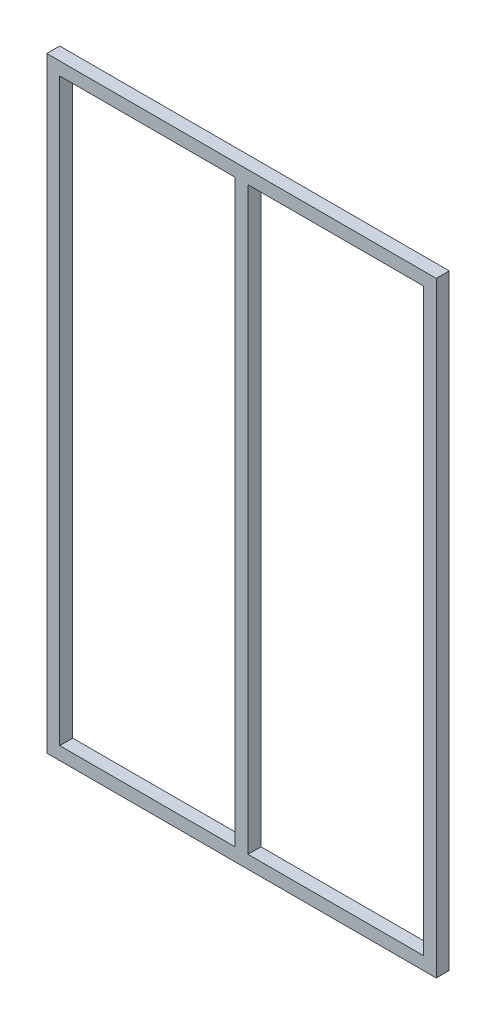
SolidWorks part; units mm, degrees
material "Cedar"
ref_plane "Front Plane" through (0, 0, 0) normal (0, 0, 1) x (1, 0, 0)
ref_plane "Top Plane" through (0, 0, 0) normal (0, 1, 0) x (1, 0, 0)
ref_plane "Right Plane" through (0, 0, 0) normal (1, 0, 0) x (0, 0, -1)
sketch "Sketch1" plane through (0, 0, 0) normal (0, 0, 1) x (1, 0, 0)
  line L1 (-285.75, -444.5) -> (285.75, -444.5)
  line L2 (-285.75, -444.5) -> (-285.75, 444.5)
  line L3 (-285.75, 444.5) -> (285.75, 444.5)
  line L4 (285.75, -444.5) -> (285.75, 444.5)
  line L5 (-285.75, -444.5) -> (285.75, 444.5) construction
  line L6 (-285.75, 444.5) -> (285.75, -444.5) construction
  point P0 (0, 0)
  dimension "D1" = 889
  dimension "D2" = 571.5
extrude "Boss-Extrude1" add sketch "Sketch1" against normal blind 19.05
sketch "Sketch2" plane through (0, 0, 0) normal (0, 0, 1) x (1, 0, 0)
  line L0 (0, 0) -> (0, 444.5) construction
  line L1 (-266.7, 425.45) -> (-9.525, 425.45)
  line L2 (-266.7, 425.45) -> (-266.7, -425.45)
  line L3 (-266.7, -425.45) -> (-9.525, -425.45)
  line L4 (-9.525, 425.45) -> (-9.525, -425.45)
  line L5 (285.75, 444.5) -> (-285.75, 444.5) construction
  line L6 (-285.75, 444.5) -> (-285.75, -444.5) construction
  line L7 (-285.75, -444.5) -> (285.75, -444.5) construction
  line L8 (9.525, 425.45) -> (9.525, -425.45)
  line L9 (266.7, -425.45) -> (9.525, -425.45)
  line L10 (266.7, 425.45) -> (266.7, -425.45)
  line L11 (266.7, 425.45) -> (9.525, 425.45)
  dimension "D1" = 19.05
  dimension "D2" = 19.05
  dimension "D3" = 19.05
  dimension "D4" = 9.525
extrude "Cut-Extrude1" cut sketch "Sketch2" against normal through all
